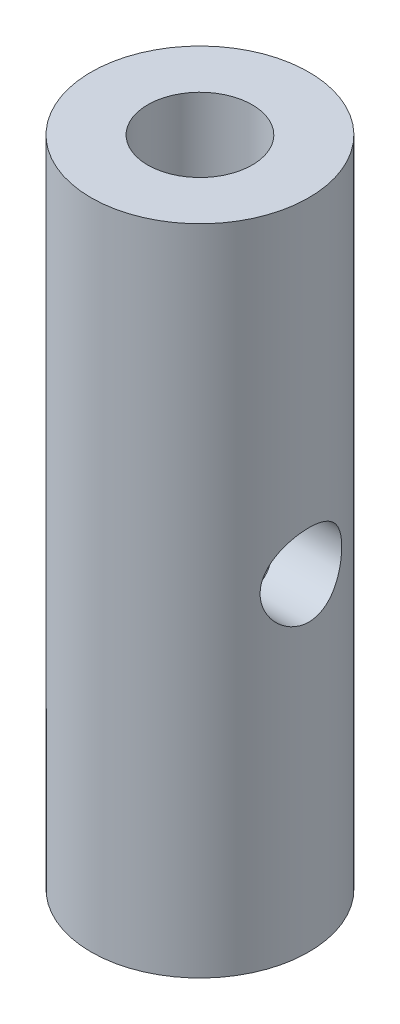
SolidWorks part; units mm, degrees
material "G-10"
ref_plane "Front Plane" through (0, 0, 0) normal (0, 0, 1) x (1, 0, 0)
ref_plane "Top Plane" through (0, 0, 0) normal (0, 1, 0) x (1, 0, 0)
ref_plane "Right Plane" through (0, 0, 0) normal (1, 0, 0) x (0, 0, -1)
sketch "Sketch1" plane through (0, 0, 0) normal (0, 1, 0) x (1, 0, 0)
  circle A0 centre (0, 0) radius 3.175
  circle A1 centre (0, 0) radius 1.5875
  dimension "D1" = 3.175
  dimension "D2" = 6.35
extrude "Boss-Extrude1" add sketch "Sketch1" along normal blind 19.05 contours A1 | A0 A1
hole_wizard "Tapped Hole for #4-40 Helicoil2" positions "Sketch4" profile "Sketch5" tap size "#4-40" standard "Helicoil® Inch"
sketch "Sketch4" plane through (0, 19.05, 0) normal (0, 1, 0) x (1, 0, 0)
  point P0 (0, 0)
cosmetic thread "Hole Thread1" parameters "D1"=5.4356, "D2"=3.7414
sketch "Sketch5" plane through (0, 19.05, 0) normal (1, 0, 0) x (0, 0, 1)
  line L0 (0, 0) -> (0, 10.5169)
  line L1 (0, 10.5169) -> (1.524, 9.6012)
  line L2 (1.524, 9.6012) -> (1.524, 0)
  line L5 (1.524, 0) -> (0, 0)
  line L10 (0, 10.5169) -> (-1.524, 9.6012) construction
  line L11 (0, -6.35) -> (0, 107.95) construction
  dimension "Tap Drill Dia." = 3.048
  dimension "Tap Drill Depth" = 9.6012
  dimension "Drill Angle" = 118
hole_wizard "3/32 (0.09375) Diameter Hole1" positions "Sketch6" profile "Sketch7" hole size "3/32" standard "ANSI Inch"
sketch "Sketch6" plane through (0, 0, 0) normal (1, 0, 0) x (0, 0, -1)
  line L0 (-3.175, 0) -> (3.175, 0) construction
  point P0 (0, 9.525)
  dimension "D1" = 9.525
sketch "Sketch7" plane through (0, 9.525, 0) normal (0, 1, 0) x (0, 0, 1)
  line L0 (0, 0) -> (0, 3.175)
  line L1 (0, 3.175) -> (1.1906, 3.175)
  line L2 (1.1906, 3.175) -> (1.1906, 0)
  line L5 (1.1906, 0) -> (0, 0)
  line L11 (0, -6.35) -> (0, 107.95) construction
  dimension "Thru Hole Dia." = 2.3812
  dimension "Thru Hole Depth" = 3.175
hole_wizard "Tapped Hole for #4-40 Helicoil3" positions "Sketch8" profile "Sketch9" tap size "#4-40" standard "Helicoil® Inch"
sketch "Sketch8" plane through (0, 0, 0) normal (0, -1, 0) x (-1, 0, 0)
  point P0 (0, 0)
sketch "Sketch9" plane through (0, 0, 0) normal (1, 0, 0) x (0, 0, -1)
  line L0 (0, 0) -> (0, 10.5169)
  line L1 (0, 10.5169) -> (1.524, 9.6012)
  line L2 (1.524, 9.6012) -> (1.524, 0)
  line L5 (1.524, 0) -> (0, 0)
  line L10 (0, 10.5169) -> (-1.524, 9.6012) construction
  line L11 (0, -6.35) -> (0, 107.95) construction
  dimension "Tap Drill Dia." = 3.048
  dimension "Tap Drill Depth" = 9.6012
  dimension "Drill Angle" = 118
cosmetic thread "Hole Thread2" parameters "D1"=5.4356, "D2"=3.7414
